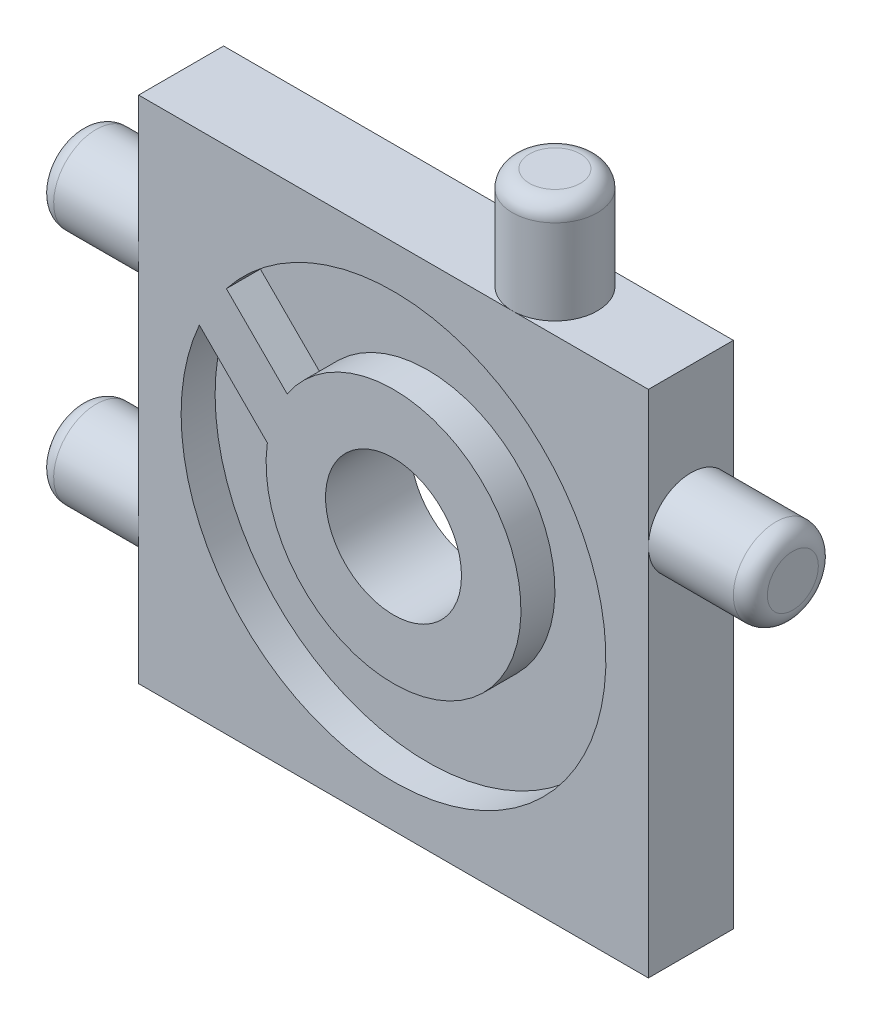
SolidWorks part; units mm, degrees
ref_plane "Plan de face" through (0, 0, 0) normal (0, 0, 1) x (1, 0, 0)
ref_plane "Plan de dessus" through (0, 0, 0) normal (0, 1, 0) x (1, 0, 0)
ref_plane "Plan de droite" through (0, 0, 0) normal (1, 0, 0) x (0, 0, -1)
sketch "Esquisse2" plane through (0, 0, 0) normal (0, 0, 1) x (1, 0, 0)
  line L1 (-15, 15) -> (15, 15)
  line L2 (-15, 15) -> (-15, -15)
  line L3 (-15, -15) -> (15, -15)
  line L4 (15, 15) -> (15, -15)
  line L5 (-15, 15) -> (15, -15) construction
  line L6 (-15, -15) -> (15, 15) construction
  point P0 (0, 0)
  dimension "D1" = 30
  dimension "D2" = 30
extrude "Boss.-Extru.1" add sketch "Esquisse2" along normal blind 5 contours L1 L4 L3 L2
sketch "Esquisse8" plane through (0, 0, 5) normal (0, 0, 1) x (1, 0, 0)
  circle A0 centre (0, 0) radius 12.5
  dimension "D1" = 25
sketch "Esquisse16" plane through (-15, 0, 0) normal (-1, 0, 0) x (0, 0, 1)
  line L0 (2.5, 15) -> (2.5, -15) construction
  line L1 (5, 15) -> (0, 15) construction
  line L2 (5, -15) -> (0, -15) construction
  circle A0 centre (2.5, 7) radius 2.5
  circle A1 centre (2.5, -7) radius 2.5
  dimension "D3" = 5
  dimension "D4" = 5
  dimension "D1" = 8
  dimension "D2" = 8
extrude "Boss.-Extru.7" add sketch "Esquisse16" along normal blind 6
fillet "Congé3" radius 1 2 edges at (-21, -9.5, 2.5) (-21, 4.5, 2.5)
sketch "Esquisse18" plane through (15, 0, 0) normal (1, 0, 0) x (0, 0, -1)
  line L0 (-2.5, -15) -> (-2.5, 15) construction
  line L1 (-5, -15) -> (0, -15) construction
  line L2 (-5, 15) -> (0, 15) construction
  circle A0 centre (-2.5, 7) radius 2.5
  dimension "D2" = 5
  dimension "D1" = 8
extrude "Boss.-Extru.9" add sketch "Esquisse18" along normal blind 6
fillet "Congé5" radius 1 1 edges at (21, 9.5, 2.5)
extrude "Enlèv. mat.-Extru.1" cut sketch "Esquisse8" against normal blind 2 contours A0
sketch "Esquisse19" plane through (0, 0, 3) normal (0, 0, 1) x (1, 0, 0)
  circle A0 centre (0, 0) radius 7.5
  dimension "D1" = 15
extrude "Boss.-Extru.10" add sketch "Esquisse19" along normal blind 2
sketch "Esquisse31" plane through (0, 0, 3) normal (0, 0, 1) x (1, 0, 0)
  line L0 (-15, 15) -> (15, -15) construction
  line L1 (15, 15) -> (-15, -15) construction
  line L2 (-12.0208, 5.6569) -> (-9.8995, 7.7782)
  line L3 (-9.8995, 7.7782) -> (-4.9373, 2.816)
  line L4 (-9.8995, 7.7782) -> (-10.0055, 7.8953)
  line L5 (-7.0587, 0.6947) -> (-4.9373, 2.816)
  line L6 (-12.0208, 5.6569) -> (-7.0587, 0.6947)
  dimension "D1" = 3
  dimension "D2" = 1.5
  dimension "D3" = 5.4825
sketch "Esquisse33" plane through (0, 0, 5) normal (0, 0, 1) x (1, 0, 0)
  circle A0 centre (0, 0) radius 4
extrude "Enlèv. mat.-Extru.3" cut sketch "Esquisse33" against normal through all
sketch "Esquisse35" plane through (0, 15, 0) normal (0, 1, 0) x (1, 0, 0)
  line L0 (-15, -2.5) -> (15, -2.5) construction
  line L1 (-15, -5) -> (-15, 0) construction
  line L2 (15, -5) -> (15, 0) construction
  circle A0 centre (7, -2.5) radius 2.5
  dimension "D1" = 8
extrude "Boss.-Extru.26" add sketch "Esquisse35" along normal blind 6
fillet "Congé6" radius 1 1 edges at (7, 21, 5)
extrude "Boss.-Extru.27" add sketch "Esquisse31" along normal blind 2 and the other way blind 5.5 contours L3 L5 L6 L2
